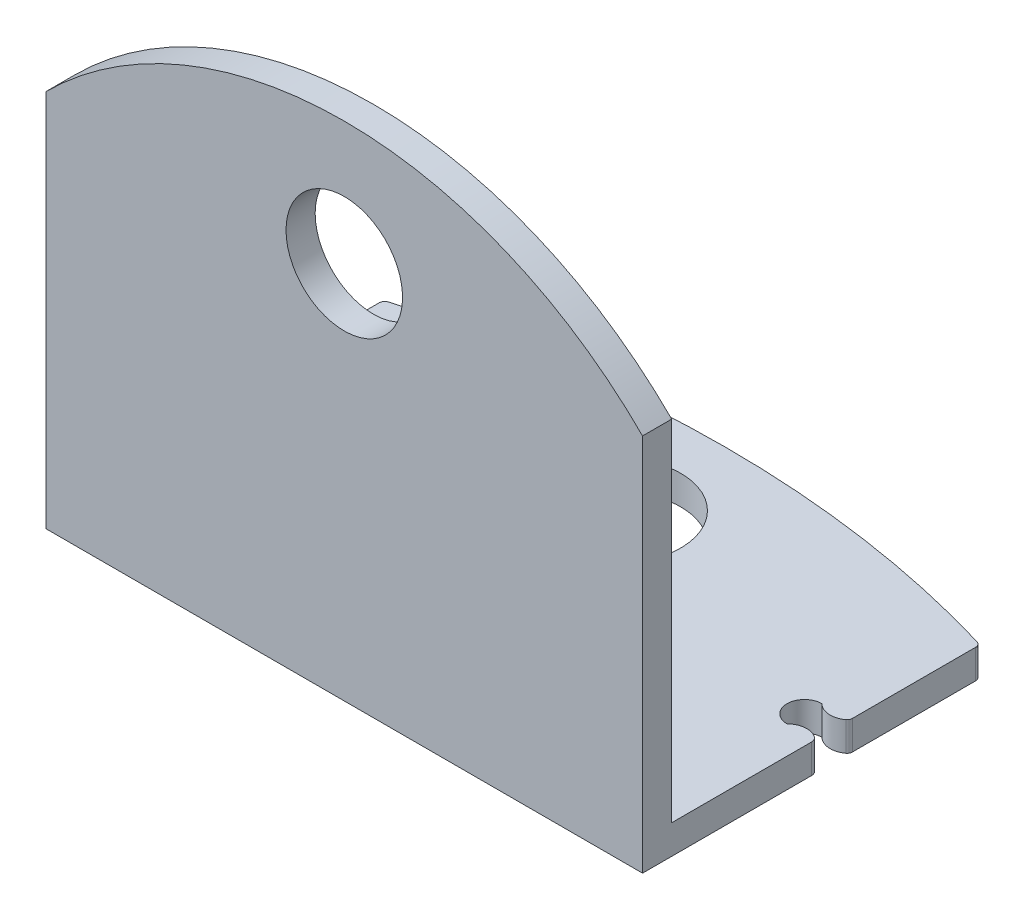
SolidWorks part; units mm, degrees
ref_plane "Alzado" through (0, 0, 0) normal (0, 0, 1) x (1, 0, 0)
ref_plane "Planta" through (0, 0, 0) normal (0, 1, 0) x (1, 0, 0)
ref_plane "Vista lateral" through (0, 0, 0) normal (1, 0, 0) x (0, 0, -1)
sketch "Croquis1" plane through (0, 0, 0) normal (0, 1, 0) x (1, 0, 0)
  line L0 (-41.1121, 5.3376) -> (-41.1121, 1.1058)
  line L1 (-41.1121, -0.2962) -> (-41.1121, -5.8412)
  line L2 (-61.3376, -6.0956) -> (-41.3665, -6.0956)
  line L3 (-61.5921, 5.3376) -> (-61.5921, 1.1058)
  line L4 (-61.5921, -5.8412) -> (-61.5921, -0.2962)
  arc A0 (-41.2552, 5.5294) -> (-61.4489, 5.5294) centre (-51.3521, -28.5205) ccw
  arc A1 (-60.6321, -0.1756) -> (-60.6321, 1.0244) centre (-60.6321, 0.4244) ccw
  arc A2 (-41.2552, 5.5294) -> (-41.1121, 5.3376) centre (-41.3121, 5.3376) cw
  arc A3 (-61.5921, 5.3376) -> (-61.4489, 5.5294) centre (-61.3921, 5.3376) cw
  circle A4 centre (-51.3521, 3.2217) radius 2.2286
  arc A17 (-61.5921, -5.8412) -> (-61.3376, -6.0956) centre (-61.3376, -5.8412) ccw
  arc A20 (-61.4729, -0.0806) -> (-60.6321, -0.1756) centre (-61.1121, -0.6556) cw
  arc A21 (-61.5203, 0.962) -> (-60.6321, 1.0244) centre (-61.1121, 1.5044) ccw
  arc A22 (-61.4729, -0.0806) -> (-61.5921, -0.2962) centre (-61.3376, -0.2962) ccw
  arc A40 (-61.5921, 1.1058) -> (-61.5203, 0.962) centre (-61.4121, 1.1058) ccw
  arc A53 (-41.1121, 1.1058) -> (-41.1838, 0.962) centre (-41.2921, 1.1058) cw
  arc A71 (-41.2313, -0.0806) -> (-41.1121, -0.2962) centre (-41.3665, -0.2962) cw
  arc A72 (-41.1838, 0.962) -> (-42.0721, 1.0244) centre (-41.5921, 1.5044) cw
  arc A73 (-41.2313, -0.0806) -> (-42.0721, -0.1756) centre (-41.5921, -0.6556) ccw
  arc A76 (-41.1121, -5.8412) -> (-41.3665, -6.0956) centre (-41.3665, -5.8412) cw
  arc A92 (-42.0721, -0.1756) -> (-42.0721, 1.0244) centre (-42.0721, 0.4244) cw
  point P103 (-41.1121, 5.6244)
  dimension "D3" = 0.2545
extrude "Saliente-Extruir1" add sketch "Croquis1" along normal blind 1
sketch "Croquis3" plane through (0, 0, 6.0956) normal (0, 0, 1) x (1, 0, 0)
  line L0 (-61.5921, 0) -> (-61.5921, 13)
  line L1 (-41.1121, 0) -> (-41.1121, 13)
  line L2 (-61.5921, 0) -> (-41.1121, 0)
  arc A0 (-61.5921, 13) -> (-41.1121, 13) centre (-51.3521, 2.76) cw
extrude "Saliente-Extruir2" add sketch "Croquis3" against normal blind 1
sketch "Croquis4" plane through (0, 0, 5.0956) normal (0, 0, -1) x (-1, 0, 0)
  circle A0 centre (51.3521, 13) radius 2
extrude "Cortar-Extruir1" cut sketch "Croquis4" against normal blind 7
